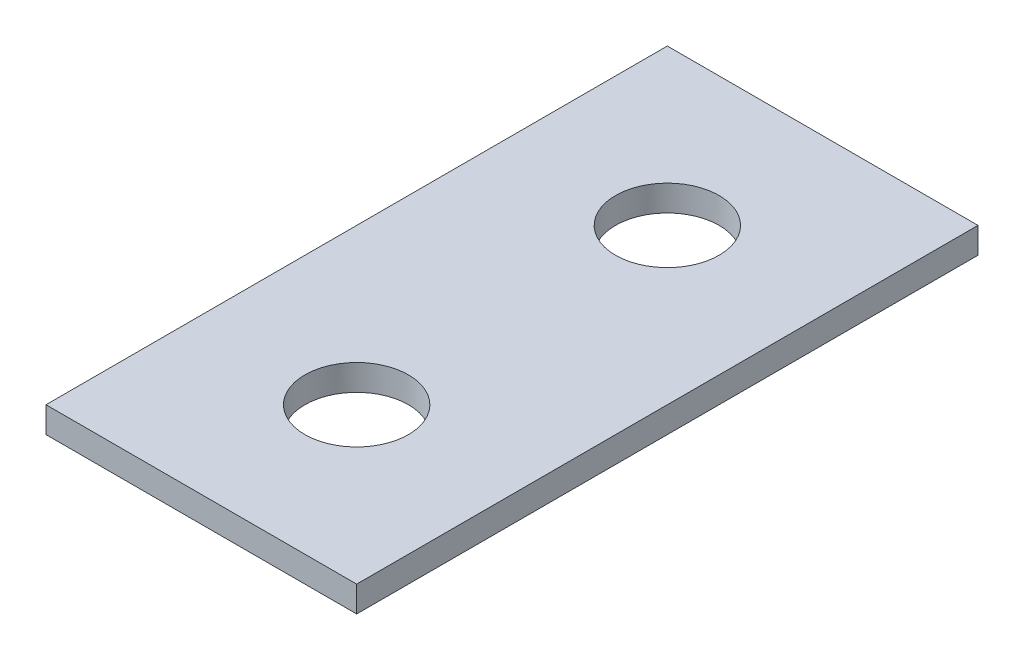
SolidWorks part; units mm, degrees
ref_plane "Front Plane" through (0, 0, 0) normal (0, 0, 1) x (1, 0, 0)
ref_plane "Top Plane" through (0, 0, 0) normal (0, 1, 0) x (1, 0, 0)
ref_plane "Right Plane" through (0, 0, 0) normal (1, 0, 0) x (0, 0, -1)
sketch "Sketch1" plane through (0, 0, 0) normal (0, 1, 0) x (1, 0, 0)
  line L1 (0, 0) -> (76.2, 0)
  line L2 (0, 0) -> (0, 152.4)
  line L3 (0, 152.4) -> (76.2, 152.4)
  line L4 (76.2, 0) -> (76.2, 152.4)
  dimension "D1" = 152.4
  dimension "D2" = 76.2
extrude "Boss-Extrude1" add sketch "Sketch1" along normal blind 6.35
hole_wizard "1 (1) Diameter Hole1" positions "Sketch3" profile "Sketch2" hole size "1" standard "Ansi Inch"
sketch "Sketch3" plane through (0, 6.35, 0) normal (0, 1, 0) x (-1, 0, 0)
  line L0 (-76.2, 0) -> (-76.2, -152.4) construction
  line L1 (-76.2, -152.4) -> (0, -152.4) construction
  line L2 (0, 0) -> (-76.2, 0) construction
  point P0 (-38.1, -38.1)
  point P1 (-38.1, -114.3)
  dimension "D1" = 38.1
  dimension "D2" = 38.1
  dimension "D3" = 38.1
  dimension "D4" = 38.1
sketch "Sketch2" plane through (38.1, 6.35, -38.1) normal (1, 0, 0) x (0, 0, 1)
  line L0 (0, 0) -> (0, 28.2049)
  line L1 (0, 28.2049) -> (12.7, 20.574)
  line L2 (12.7, 20.574) -> (12.7, 0)
  line L5 (12.7, 0) -> (0, 0)
  line L10 (0, 28.2049) -> (-12.7, 20.574) construction
  line L11 (0, -6.35) -> (0, 107.95) construction
  dimension "Hole Dia." = 25.4
  dimension "Hole Depth" = 20.574
  dimension "Drill Angle" = 118
